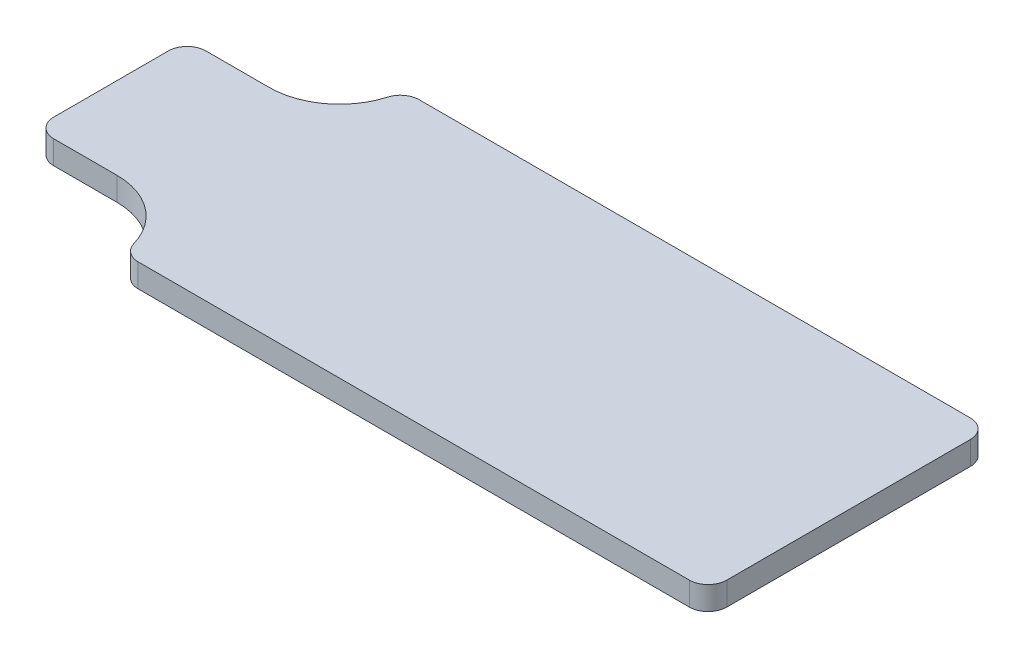
SolidWorks part; units mm, degrees
ref_plane "Front Plane" through (0, 0, 0) normal (0, 0, 1) x (1, 0, 0)
ref_plane "Top Plane" through (0, 0, 0) normal (0, 1, 0) x (1, 0, 0)
ref_plane "Right Plane" through (0, 0, 0) normal (1, 0, 0) x (0, 0, -1)
sketch "Sketch1" plane through (0, 0, 0) normal (0, 1, 0) x (1, 0, 0)
  line L1 (-65, 92.5) -> (-30, 92.5)
  line L2 (-65, 92.5) -> (-65, 27.5)
  line L3 (-65, 27.5) -> (-30, 27.5)
  line L5 (0, 120) -> (250, 120)
  line L7 (0, 0) -> (250, 0)
  line L8 (250, 120) -> (250, 0)
  arc A0 (-30, 92.5) -> (0, 120) centre (-30, 122.6136) ccw
  arc A1 (-30, 27.5) -> (0, 0) centre (-30, -2.6136) cw
  point P8 (-65, 60)
  point P9 (250, 60)
  dimension "D1" = 65
  dimension "D2" = 35
  dimension "D3" = 120
  dimension "D4" = 250
  dimension "D5" = 30
  dimension "D6" = 35
  dimension "D7" = 250
extrude "Boss-Extrude1" add sketch "Sketch1" along normal blind 10
fillet "Fillet1" radius 8 6 edges at (0, 5, 0) (250, 5, 0) (250, 5, -120) (0, 5, -120) (-65, 5, -92.5) (-65, 5, -27.5)
